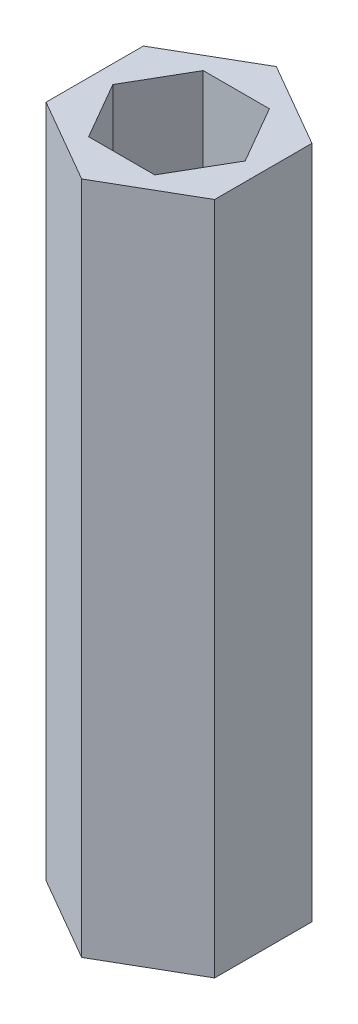
SolidWorks part; units mm, degrees
material "PET"
ref_plane "Front" through (0, 0, 0) normal (0, 0, 1) x (1, 0, 0)
ref_plane "Top" through (0, 0, 0) normal (0, 1, 0) x (1, 0, 0)
ref_plane "Right" through (0, 0, 0) normal (1, 0, 0) x (0, 0, -1)
sketch "Sketch1" plane through (0, 0, 0) normal (0, 1, 0) x (1, 0, 0)
  line L1 (3.7395, 6.477) -> (-3.7395, 6.477)
  line L2 (-3.7395, 6.477) -> (-7.479, 0)
  line L3 (-7.479, 0) -> (-3.7395, -6.477)
  line L4 (-3.7395, -6.477) -> (3.7395, -6.477)
  line L5 (3.7395, -6.477) -> (7.479, 0)
  line L6 (7.479, 0) -> (3.7395, 6.477)
  line L7 (0, -10.9985) -> (9.525, -5.4993)
  line L8 (9.525, -5.4993) -> (9.525, 5.4993)
  line L9 (9.525, 5.4993) -> (0, 10.9985)
  line L10 (0, 10.9985) -> (-9.525, 5.4993)
  line L11 (-9.525, 5.4993) -> (-9.525, -5.4993)
  line L12 (-9.525, -5.4993) -> (0, -10.9985)
  circle A1 centre (0, 0) radius 6.477 construction
  circle A2 centre (0, 0) radius 9.525 construction
  dimension "D2" = 19.05
  dimension "D1" = 12.954
extrude "Boss-Extrude1" add sketch "Sketch1" along normal blind 76.2
